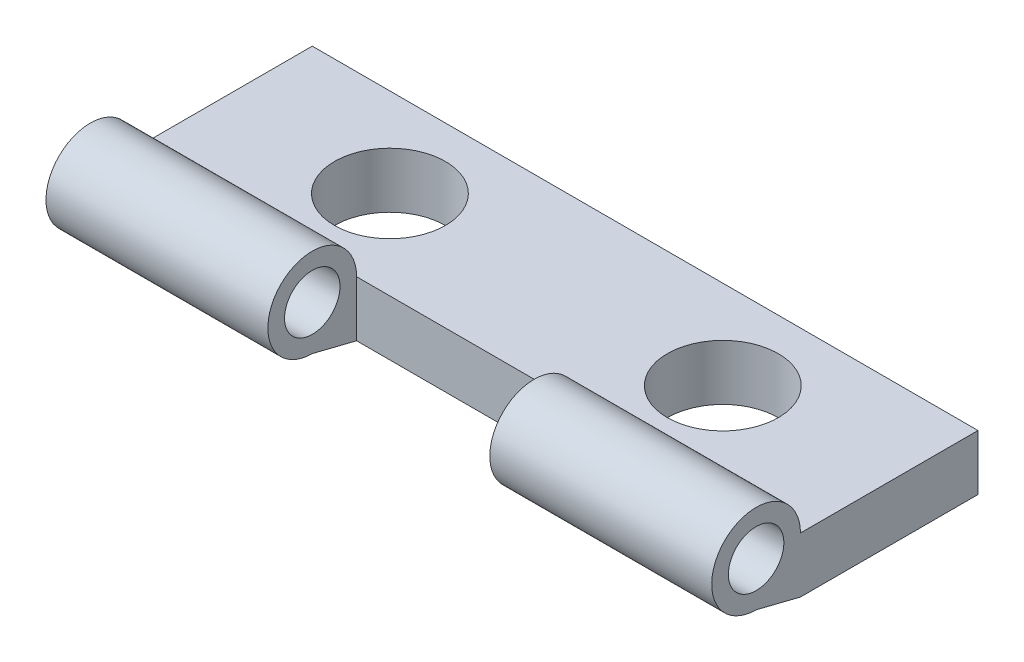
SolidWorks part; units mm, degrees
material "1060 Alloy"
ref_plane "Front Plane" through (0, 0, 0) normal (0, 0, 1) x (1, 0, 0)
ref_plane "Top Plane" through (0, 0, 0) normal (0, 1, 0) x (1, 0, 0)
ref_plane "Right Plane" through (0, 0, 0) normal (1, 0, 0) x (0, 0, -1)
sketch "Sketch1" plane through (0, 0, 0) normal (0, 1, 0) x (1, 0, 0)
  line L1 (-15, -4) -> (15, -4)
  line L2 (-15, -4) -> (-15, 4)
  line L3 (-15, 4) -> (15, 4)
  line L4 (15, -4) -> (15, 4)
  line L5 (-15, -4) -> (15, 4) construction
  line L6 (-15, 4) -> (15, -4) construction
  circle A0 centre (-7.5, 0) radius 2.5
  circle A1 centre (7.5, 0) radius 2.5
  point P0 (0, 0)
  dimension "D5" = 5
  dimension "D1" = 30
  dimension "D2" = 8
  dimension "D3" = 7.5
  dimension "D4" = 7.5
extrude "Boss-Extrude1" add sketch "Sketch1" along normal blind 2.5
sketch "Sketch2" plane through (0, 0, 0) normal (1, 0, 0) x (0, 0, -1)
  line L0 (0, 0) -> (0, 2.5) construction
  line L1 (-4, 2.5) -> (4, 2.5) construction
  line L5 (-4, 2.5) -> (-4, 0)
  line L6 (-4, 0) -> (-6, 0.5)
  circle A1 centre (-6, 2.5) radius 1.25
  arc A2 (-4, 2.5) -> (-6, 0.5) centre (-6, 2.5) ccw
  dimension "D1" = 4
  dimension "D2" = 2.5
extrude "Boss-Extrude2" add sketch "Sketch2" along normal up to surface and the other way up to surface up to face at (15, 1.25, 0) other way up to face at (-15, 1.25, 0)
sketch "Sketch4" plane through (0, 0, 0) normal (0, 1, 0) x (1, 0, 0)
  line L0 (-15, -4) -> (15, -4) construction
  line L2 (-5, -4) -> (-5, -8)
  line L4 (5, -4) -> (5, -8)
  line L5 (-15, -8) -> (15, -8) construction
  line L6 (15, -8) -> (15, -4) construction
  line L13 (-5, -8) -> (5, -8)
  line L14 (5, -4) -> (-5, -4)
  dimension "D1" = 10
  dimension "D2" = 10
extrude "Cut-Extrude2" cut sketch "Sketch4" along normal through all
